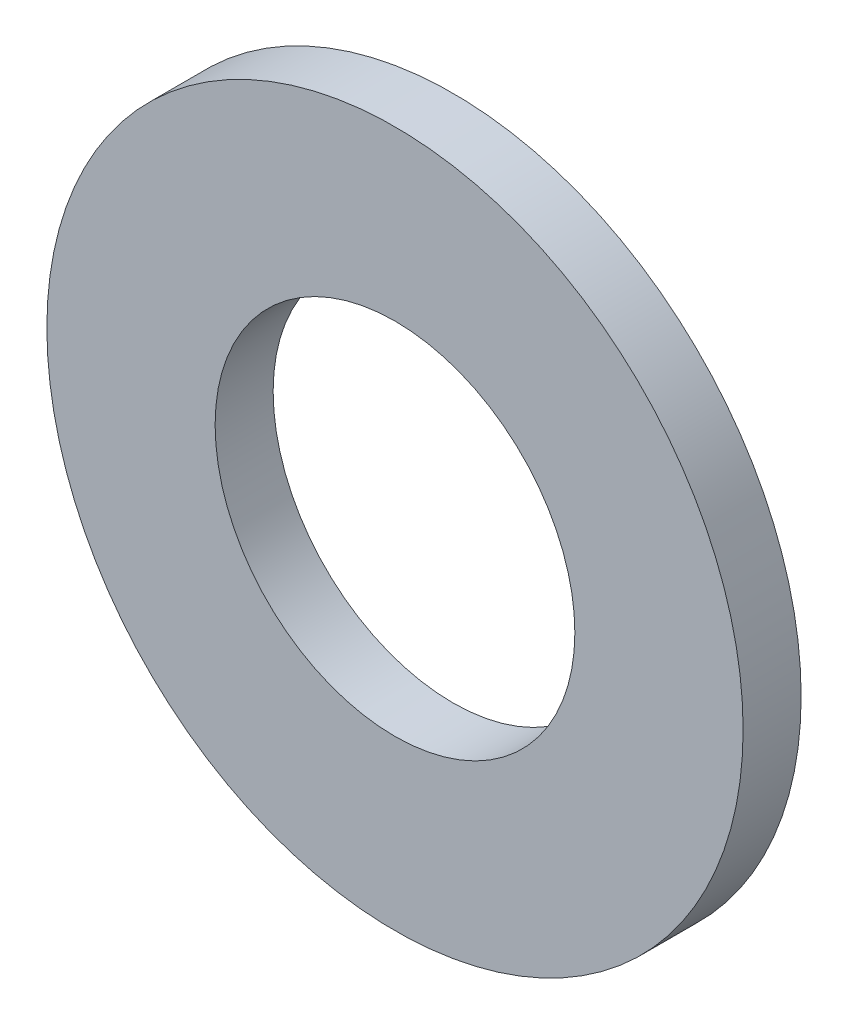
SolidWorks part; units mm, degrees
ref_plane "Front Plane" through (0, 0, 0) normal (0, 0, 1) x (1, 0, 0)
ref_plane "Top Plane" through (0, 0, 0) normal (0, 1, 0) x (1, 0, 0)
ref_plane "Right Plane" through (0, 0, 0) normal (1, 0, 0) x (0, 0, -1)
sketch "Sketch1" plane through (0, 0, 0) normal (0, 0, 1) x (1, 0, 0)
  circle A0 centre (0, 0) radius 3
  circle A1 centre (0, 0) radius 1.55
  dimension "D1" = 3.1
  dimension "D2" = 6
extrude "Boss-Extrude1" add sketch "Sketch1" along normal blind 0.5
